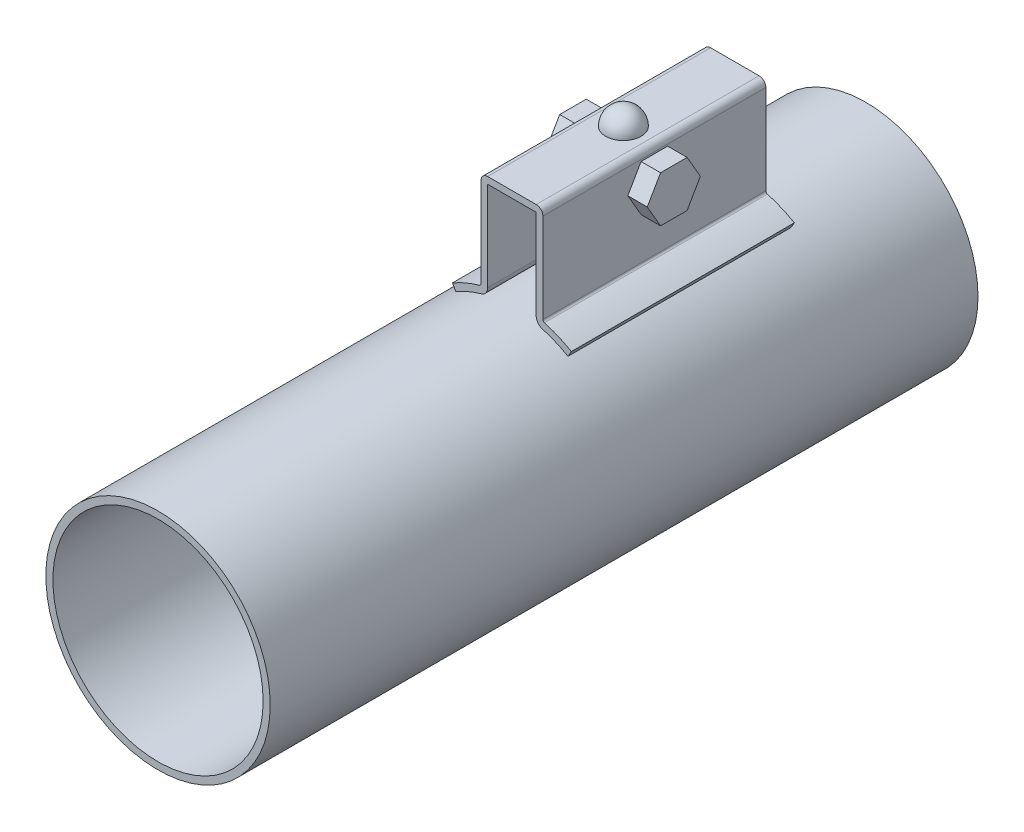
SolidWorks part; units mm, degrees
ref_plane "Front Plane" through (0, 0, 0) normal (0, 0, 1) x (1, 0, 0)
ref_plane "Top Plane" through (0, 0, 0) normal (0, 1, 0) x (1, 0, 0)
ref_plane "Right Plane" through (0, 0, 0) normal (1, 0, 0) x (0, 0, -1)
sketch "Sketch1" plane through (0, 0, 0) normal (0, 0, 1) x (1, 0, 0)
  circle A0 centre (0, 0) radius 31.7
  circle A1 centre (0, 0) radius 29.7
  dimension "D1" = 2
  dimension "D2" = 63.4
extrude "Boss-Extrude1" add sketch "Sketch1" along normal blind 200
ref_plane "Plane1" through (0, 0, 100) normal (0, 0, -1) x (-1, 0, 0)
sketch "Sketch4" plane through (0, 0, 100) normal (0, 0, -1) x (-1, 0, 0)
  line L1 (-6.85, 32.8971) -> (-6.85, 58.2)
  line L2 (-6.85, 58.2) -> (6.85, 58.2)
  line L3 (6.85, 58.2) -> (6.85, 32.8971)
  line L4 (15.85, 27.453) -> (16.8, 29.0985)
  line L5 (8.75, 32.8971) -> (8.75, 58.2)
  line L6 (6.85, 60.1) -> (-6.85, 60.1)
  line L7 (-8.75, 58.2) -> (-8.75, 32.8971)
  line L8 (6.85, 58.2) -> (8.75, 58.2) construction
  line L9 (-6.85, 58.2) -> (-8.75, 58.2) construction
  line L10 (0, 58.2) -> (0, 60.1) construction
  line L11 (-15.85, 27.453) -> (-16.8, 29.0985)
  arc A1 (-8.6665, 30.4923) -> (-6.85, 32.8971) centre (-9.35, 32.8971) ccw
  arc A2 (6.85, 32.8971) -> (8.6665, 30.4923) centre (9.35, 32.8971) ccw
  arc A3 (8.6665, 30.4923) -> (15.85, 27.453) centre (0, 0) cw
  arc A4 (16.8, 29.0985) -> (9.186, 32.3199) centre (0, 0) ccw
  arc A5 (9.186, 32.3199) -> (8.75, 32.8971) centre (9.35, 32.8971) cw
  arc A6 (8.75, 58.2) -> (6.85, 60.1) centre (6.85, 58.2) ccw
  arc A7 (-6.85, 60.1) -> (-8.75, 58.2) centre (-6.85, 58.2) ccw
  arc A8 (-8.75, 32.8971) -> (-9.186, 32.3199) centre (-9.35, 32.8971) cw
  circle A10 centre (0, 0) radius 31.7 construction
  circle A11 centre (0, 0) radius 31.7 construction
  arc A12 (-8.6665, 30.4923) -> (-15.85, 27.453) centre (0, 0) ccw
  arc A13 (-16.8, 29.0985) -> (-9.186, 32.3199) centre (0, 0) cw
  point P35 (0, 60.1)
  dimension "D4" = 2.5
  dimension "D1" = 28.4
  dimension "D2" = 1.9
  dimension "D3" = 17.5
  dimension "D5" = 60
extrude "Boss-Extrude2" add sketch "Sketch4" along normal blind 63
ref_plane "Plane2" through (0, 0, 0) normal (-1, 0, 0) x (0, 0, 1)
sketch "Sketch5" plane through (0, 0, 0) normal (-1, 0, 0) x (0, 0, 1)
  line L0 (63.5, 60.1) -> (73.5, 60.1)
  line L1 (37, 60.1) -> (100, 60.1) construction
  line L2 (37, 60.1) -> (100, 60.1) construction
  line L3 (68.5, 60.1) -> (68.5, 65.1)
  arc A0 (73.5, 60.1) -> (63.5, 60.1) centre (68.5, 60.1) ccw
  dimension "D1" = 10
revolve "Revolve1" add sketch "Sketch5" angle 360 about L3
sketch "Sketch6" plane through (-8.75, 0, 0) normal (-1, 0, 0) x (0, 0, 1)
  line L0 (37, 32.8971) -> (100, 32.8971) construction
  line L1 (72.2528, 44.7) -> (76.0056, 51.2)
  line L2 (76.0056, 51.2) -> (72.2528, 57.7)
  line L3 (72.2528, 57.7) -> (64.7472, 57.7)
  line L4 (64.7472, 57.7) -> (60.9944, 51.2)
  line L5 (60.9944, 51.2) -> (64.7472, 44.7)
  line L6 (64.7472, 44.7) -> (72.2528, 44.7)
  line L7 (37, 32.8971) -> (100, 32.8971) construction
  line L8 (37, 58.2) -> (100, 58.2) construction
  circle A0 centre (68.5, 51.2) radius 6.5 construction
  point P11 (68.5, 32.8971)
  dimension "D1" = 13
  dimension "D2" = 7
extrude "Boss-Extrude3" add sketch "Sketch6" along normal blind 5.5 and the other way offset from surface (23 mm away) 5.5 other way up to face at (8.75, 45.5485, 68.5)
